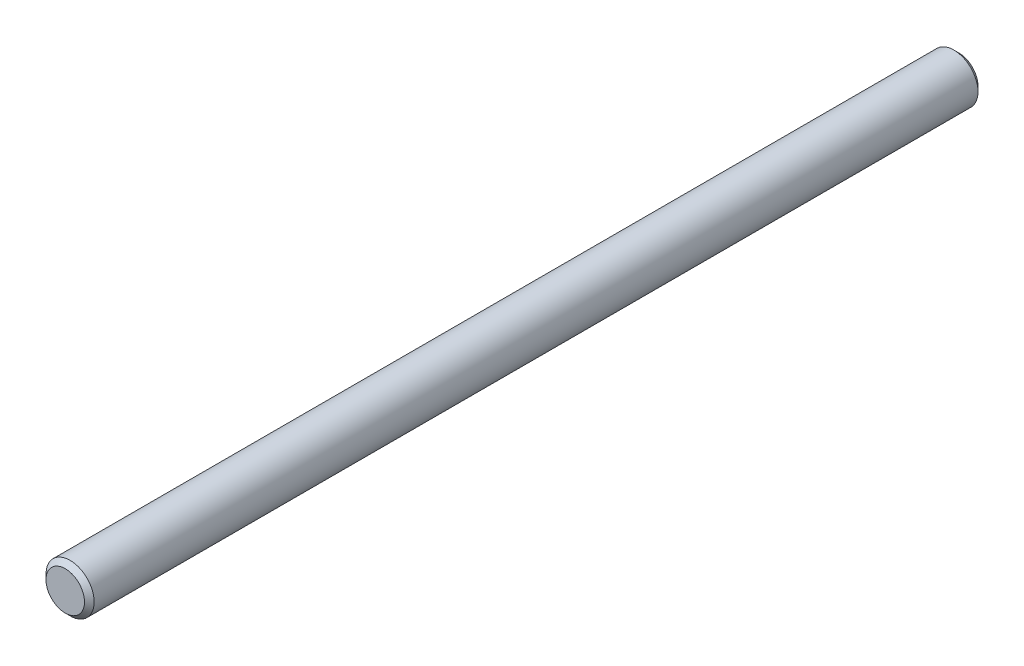
SolidWorks part; units mm, degrees
ref_plane "Front" through (0, 0, 0) normal (0, 0, 1) x (1, 0, 0)
ref_plane "Top" through (0, 0, 0) normal (0, 1, 0) x (1, 0, 0)
ref_plane "Right" through (0, 0, 0) normal (1, 0, 0) x (0, 0, -1)
sketch "Sketch1" plane through (0, 0, 0) normal (0, 0, 1) x (1, 0, 0)
  circle A0 centre (0, 0) radius 15.875
  dimension "D1" = 31.75
extrude "Extrude1" add sketch "Sketch1" along normal mid plane 589.28
chamfer "Chamfer1" distance 3.175 angle 45 2 edges at (15.875, 0, -294.64) (15.875, 0, 294.64)
equation "\"D1@Chamfer1\" = \"D1@Sketch1\" * .1"
